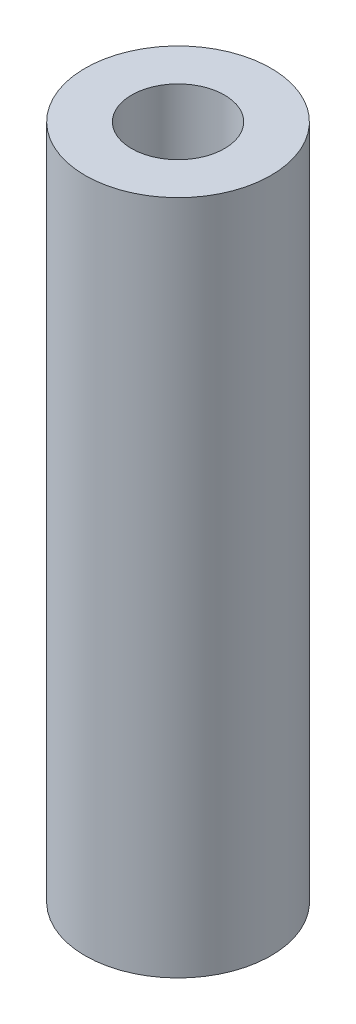
SolidWorks part; units mm, degrees
ref_plane "Front Plane" through (0, 0, 0) normal (0, 0, 1) x (1, 0, 0)
ref_plane "Top Plane" through (0, 0, 0) normal (0, 1, 0) x (1, 0, 0)
ref_plane "Right Plane" through (0, 0, 0) normal (1, 0, 0) x (0, 0, -1)
sketch "Sketch1" plane through (0, 0, 0) normal (0, 1, 0) x (1, 0, 0)
  circle A0 centre (0, 0) radius 11
  circle A1 centre (0, 0) radius 5.5
  dimension "D1" = 22
  dimension "D2" = 11
extrude "Boss-Extrude1" add sketch "Sketch1" along normal mid plane 80
